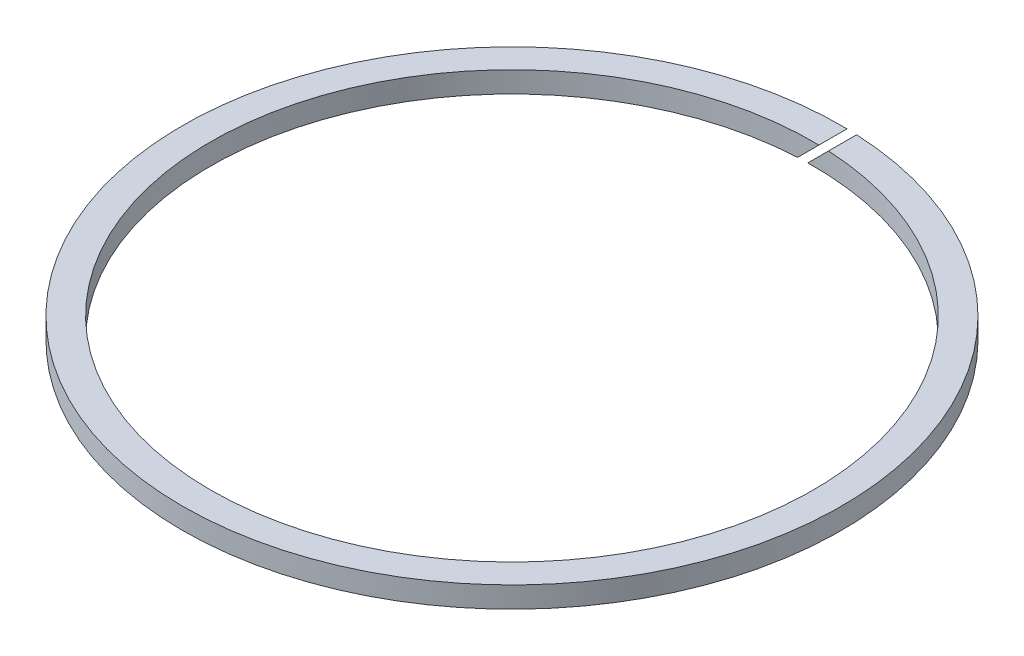
SolidWorks part; units mm, degrees
ref_plane "Front Plane" through (0, 0, 0) normal (0, 0, 1) x (1, 0, 0)
ref_plane "Top Plane" through (0, 0, 0) normal (0, 1, 0) x (1, 0, 0)
ref_plane "Right Plane" through (0, 0, 0) normal (1, 0, 0) x (0, 0, -1)
sketch "Sketch1" plane through (0, 0, 0) normal (0, 1, 0) x (1, 0, 0)
  circle A0 centre (0, 0) radius 47
  circle A1 centre (0, 0) radius 43
  dimension "D1" = 94
  dimension "D2" = 86
extrude "Boss-Extrude1" add sketch "Sketch1" along normal mid plane 3
sketch "Sketch2" plane through (0, 0, 0) normal (0, 0, 1) x (1, 0, 0)
  line L0 (-47, 0) -> (49953, 0) construction
  line L1 (-47, 1.5) -> (-47, -1.5) construction
  line L2 (-1.0583, 1.5) -> (49998.9417, 1.5) construction
  line L4 (0.7929, 1.5) -> (-2.2071, -1.5)
  line L5 (2.2071, 1.5) -> (-0.7929, -1.5)
  line L7 (-2.7808, -1.5) -> (49997.2192, -1.5) construction
  line L9 (-2.2071, -1.5) -> (-0.7929, -1.5)
  line L10 (0.7929, 1.5) -> (2.2071, 1.5)
  point P4 (-47, 0)
  point P11 (0, 0)
extrude "Cut-Extrude1" cut sketch "Sketch2" against normal through all
